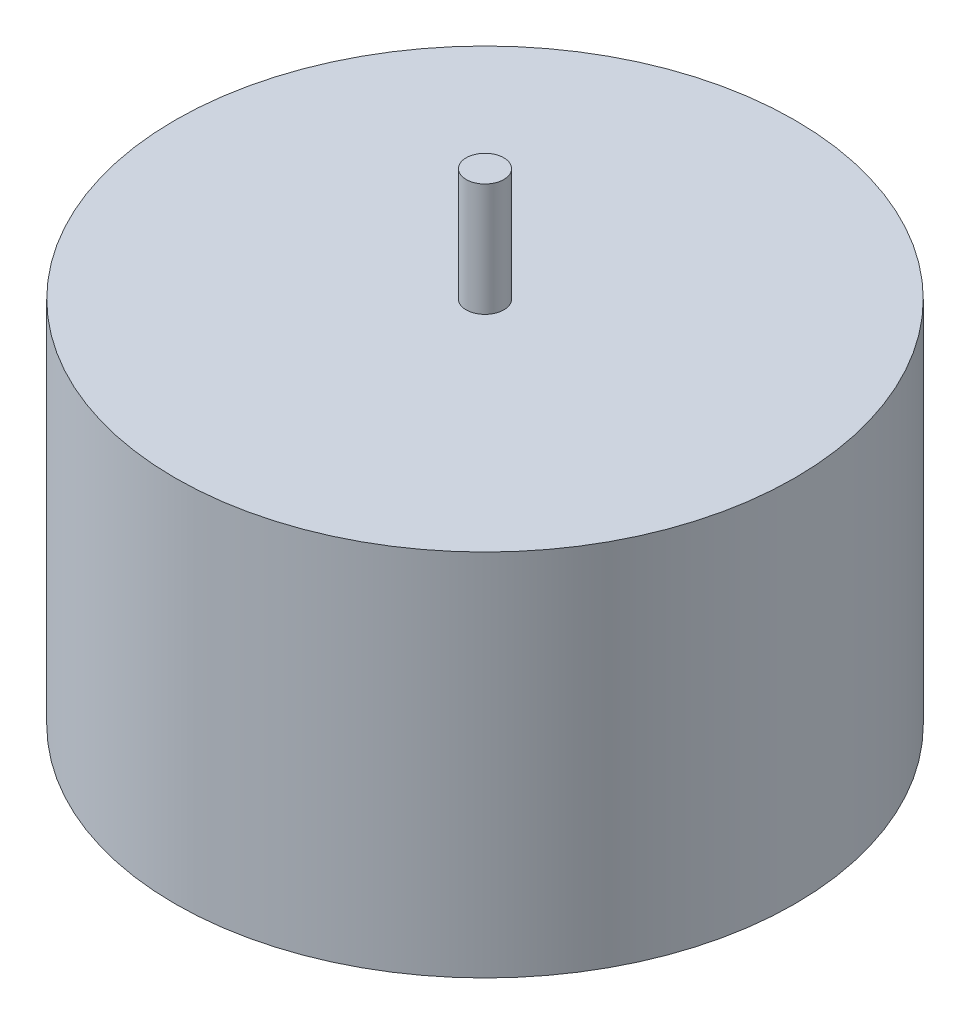
SolidWorks part; units mm, degrees
ref_plane "Front Plane" through (0, 0, 0) normal (0, 0, 1) x (1, 0, 0)
ref_plane "Top Plane" through (0, 0, 0) normal (0, 1, 0) x (1, 0, 0)
ref_plane "Right Plane" through (0, 0, 0) normal (1, 0, 0) x (0, 0, -1)
sketch "Sketch1" plane through (0, 0, 0) normal (0, 1, 0) x (1, 0, 0)
  circle A0 centre (-33.392, 17.6639) radius 12.35
  dimension "D1" = 24.7
extrude "Boss-Extrude1" add sketch "Sketch1" along normal blind 14.7
sketch "Sketch2" plane through (0, 14.7, 0) normal (0, 1, 0) x (1, 0, 0)
  line L0 (-33.392, 30.0139) -> (-33.392, 5.3139) construction
  circle A0 centre (-33.392, 17.6639) radius 12.35 construction
  circle A1 centre (-33.392, 17.6639) radius 0.75
extrude "Boss-Extrude2" add sketch "Sketch2" along normal blind 4.5 contours A1
